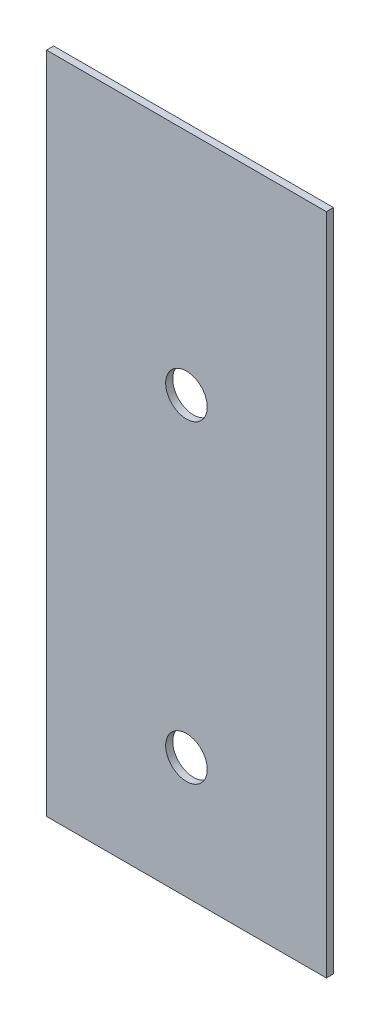
SolidWorks part; units mm, degrees
material "Pine"
ref_plane "Front Plane" through (0, 0, 0) normal (0, 0, 1) x (1, 0, 0)
ref_plane "Top Plane" through (0, 0, 0) normal (0, 1, 0) x (1, 0, 0)
ref_plane "Right Plane" through (0, 0, 0) normal (1, 0, 0) x (0, 0, -1)
sketch "Sketch1" plane through (0, 0, 0) normal (0, 0, 1) x (1, 0, 0)
  line L1 (-234.95, -557.2125) -> (234.95, -557.2125)
  line L2 (-234.95, -557.2125) -> (-234.95, 557.2125)
  line L3 (-234.95, 557.2125) -> (234.95, 557.2125)
  line L4 (234.95, -557.2125) -> (234.95, 557.2125)
  line L5 (-234.95, -557.2125) -> (234.95, 557.2125) construction
  line L6 (-234.95, 557.2125) -> (234.95, -557.2125) construction
  point P0 (0, 0)
  dimension "D1" = 1114.425
  dimension "D2" = 469.9
extrude "Boss-Extrude1" add sketch "Sketch1" along normal blind 11.9062
sketch "Sketch2" plane through (0, 0, 11.9062) normal (0, 0, 1) x (1, 0, 0)
  line L1 (-234.95, -557.2125) -> (234.95, -557.2125) construction
  point P0 (0, 173.0375)
  point P1 (0, -354.0125)
  dimension "D1" = 203.2
  dimension "D2" = 527.05
hole_wizard "2 Clearance Hole1" positions "Sketch3" profile "Sketch4" hole size "2" standard "ANSI Inch" end condition through all
sketch "Sketch3" plane through (0, 0, 11.9062) normal (0, 0, 1) x (1, 0, 0)
  point P0 (0, 173.0375)
  point P3 (0, -354.0125)
sketch "Sketch4" plane through (0, 173.0375, 11.9062) normal (1, 0, 0) x (0, -1, 0)
  line L0 (0, 0) -> (0, 11.9062)
  line L1 (0, 11.9062) -> (34.925, 11.9062)
  line L2 (34.925, 11.9062) -> (34.925, 0)
  line L5 (34.925, 0) -> (0, 0)
  line L11 (0, -6.35) -> (0, 107.95) construction
  dimension "Thru Hole Dia." = 69.85
  dimension "Thru Hole Depth" = 11.9062
